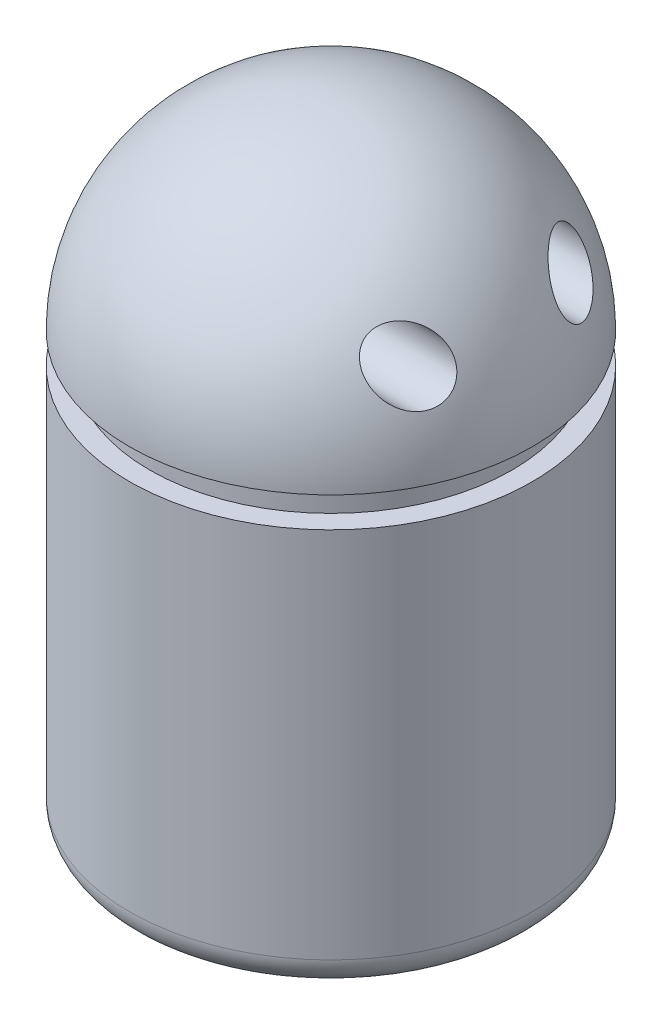
SolidWorks part; units mm, degrees
ref_plane "Alzado" through (0, 0, 0) normal (0, 0, 1) x (1, 0, 0)
ref_plane "Planta" through (0, 0, 0) normal (0, 1, 0) x (1, 0, 0)
ref_plane "Vista lateral" through (0, 0, 0) normal (1, 0, 0) x (0, 0, -1)
sketch "Croquis4" plane through (0, 0, 0) normal (0, 0, 1) x (1, 0, 0)
  line L0 (-20, 25.0872) -> (-20, -17.9128) construction
  line L1 (-20, -17.9128) -> (0, -17.9128) construction
  line L2 (20, -17.9128) -> (20, 22.0839)
  line L3 (0, 45.0872) -> (0, -17.9128)
  line L4 (0, -17.9128) -> (20, -17.9128)
  line L5 (20, 25.0872) -> (18, 25.0872)
  line L6 (18, 25.0872) -> (18, 22.0839)
  line L7 (18, 22.0839) -> (20, 22.0839)
  arc A0 (20, 25.0872) -> (0, 45.0872) centre (0, 25.0872) ccw
  arc A1 (-20, 25.0872) -> (0, 45.0872) centre (0, 25.0872) cw construction
  dimension "D1" = 63
  dimension "D4" = 2
  dimension "D2" = 20
  dimension "D3" = 43
  dimension "D5" = 3.0033
revolve "Revolución4" add sketch "Croquis4" angle 360 about L3
fillet "Redondeo3" radius 3 1 edges at (-20, -17.9128, 0)
sketch "Croquis9" plane through (0, 0, 0) normal (1, 0, 0) x (0, 0, -1)
  line L0 (0, 60.2525) -> (0, -25.4873) construction
  circle A1 centre (8, 33.8856) radius 3
  circle A2 centre (-8, 33.8856) radius 3
  dimension "D1" = 8
extrude "Cortar-Extruir3" cut sketch "Croquis9" along normal blind 18
